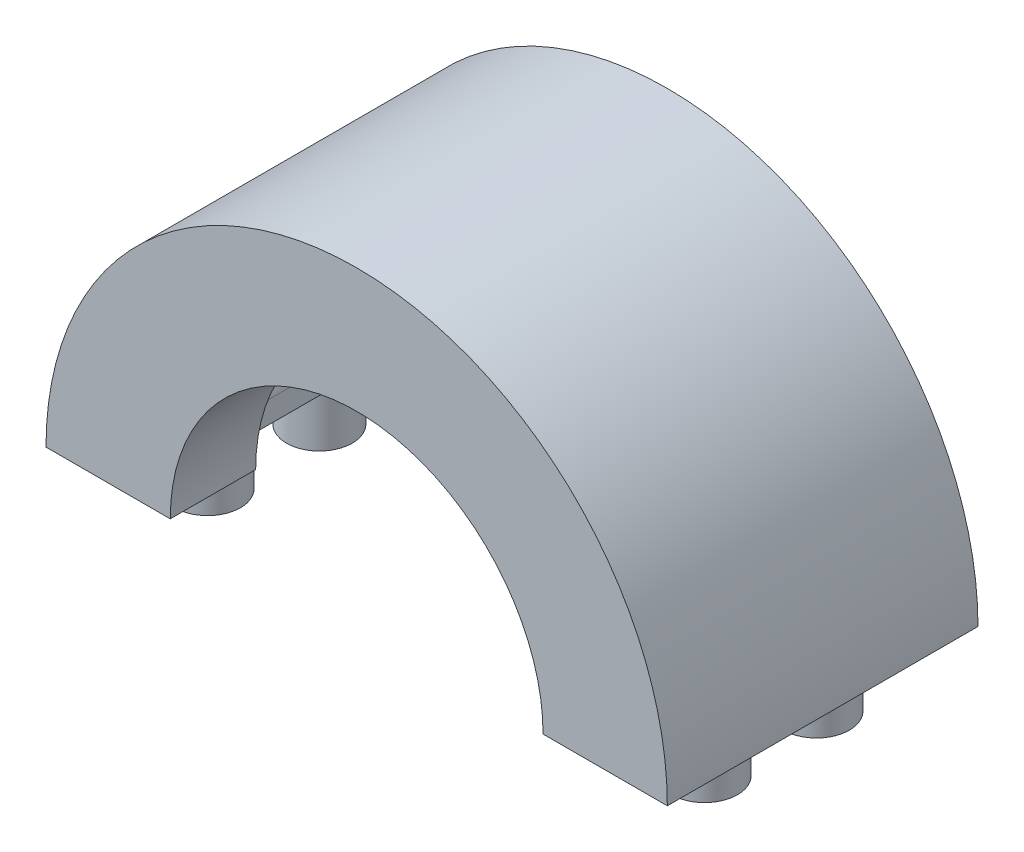
SolidWorks part; units mm, degrees
ref_plane "Front Plane" through (0, 0, 0) normal (0, 0, 1) x (1, 0, 0)
ref_plane "Top Plane" through (0, 0, 0) normal (0, 1, 0) x (1, 0, 0)
ref_plane "Right Plane" through (0, 0, 0) normal (1, 0, 0) x (0, 0, -1)
sketch "Sketch1" plane through (0, 0, 0) normal (0, 0, 1) x (1, 0, 0)
  line L0 (0, 0) -> (49.1339, 0) construction
  line L1 (49.1339, 0) -> (-47.428, 0) construction
  line L2 (-25, 0) -> (-15, 0)
  line L3 (15, 0) -> (25, 0)
  arc A0 (15, 0) -> (-15, 0) centre (0, 0) ccw
  arc A1 (25, 0) -> (-25, 0) centre (0, 0) ccw
  dimension "D1" = 50
  dimension "D2" = 30
extrude "Boss-Extrude1" add sketch "Sketch1" along normal mid plane 25 contours A1 L2 A0 L3
ref_plane "Plane1" through (0, 0, 12.5) normal (0, 0, 1) x (1, 0, 0)
ref_plane "Plane2" through (0, 0, 0) normal (0, 0, -1) x (-1, 0, 0)
sketch "Sketch3" plane through (0, 0, 0) normal (0, 0, -1) x (-1, 0, 0)
  line L0 (13.75, 0) -> (-13.75, 0) construction
  line L1 (12.7119, -13.5285) -> (17.2881, -13.5285)
  line L4 (15.5936, 0) -> (15.5936, 4.536)
  line L6 (16.6576, 6.832) -> (16.6576, -49993.168) construction
  line L7 (15, 0) -> (20.7782, 0) construction
  line L8 (20.7782, 0) -> (4.4661, 0) construction
  line L9 (15, 0) -> (15.5936, 0)
  line L10 (-1032.1335, 6.888) -> (-13.325, 6.888) construction
  line L11 (38.5096, 5.712) -> (-49961.4904, 5.712) construction
  line L16 (15.5936, 4.536) -> (16.6576, 5.712)
  line L17 (15.5936, 4.536) -> (50015.5936, 4.536) construction
  line L18 (16.6576, 5.712) -> (16.6576, 8.008)
  line L20 (13.325, 6.888) -> (50005.4836, 6.888) construction
  line L21 (16.6576, 8.008) -> (12.6835, 8.008)
  arc A0 (15, 0) -> (-15, 0) centre (0, 0) ccw construction
  arc A2 (-13.325, 6.888) -> (-13.8699, 5.712) centre (0, 0) ccw
  arc A4 (-13.325, 6.888) -> (-14.2977, 4.536) centre (0, 0) ccw
  arc A6 (15, 0) -> (12.6835, 8.008) centre (0, 0) ccw
  arc A7 (-13.325, 6.888) -> (-14.2977, 4.536) centre (0, 0) ccw
  point P0 (15, 0)
  dimension "D4" = 2.296
  dimension "D1" = 0.5936
  dimension "D2" = 4.536
  dimension "D3" = 1.176
extrude "Cut-Extrude1" cut sketch "Sketch3" against normal mid plane 11.256
mirror "Mirror3" about plane through (0, 0, 0) normal (1, 0, 0) of "Cut-Extrude1"
sketch "Sketch4" plane through (0, 0, 0) normal (0, -1, 0) x (1, 0, 0)
  line L0 (-25, 0) -> (-50025, 0) construction
  line L1 (-25, 12.5) -> (-25, -12.5) construction
  line L4 (-20, -7.5) -> (-20, 49992.5) construction
  line L5 (-25, -12.5) -> (-15, -12.5) construction
  line L6 (-36.0666, 4.5) -> (49963.9334, 4.5) construction
  line L7 (35.3711, -4.5) -> (-49964.6289, -4.5) construction
  line L8 (13.75, 12.5) -> (-13.75, 12.5) construction
  circle A0 centre (-20, 4.5) radius 2.6478
  circle A1 centre (-20, -4.5) radius 2.6478
  point P4 (-25, 0)
  point P9 (-20, -12.5)
  dimension "D3" = 5.2955
  dimension "D1" = 8
fillet "Fillet5" radius 2 2 edges at (-15.5936, 4.536, 0) (15.5936, 4.536, 0)
chamfer "Chamfer9" distance 2 angle 45 2 edges at (15.5936, 0, 0) (-15.5936, 0, 0)
extrude "Boss-Extrude2" add sketch "Sketch4" along normal blind 4.4055
mirror "Mirror4" about plane through (0, 0, 0) normal (1, 0, 0) of "Boss-Extrude2"
